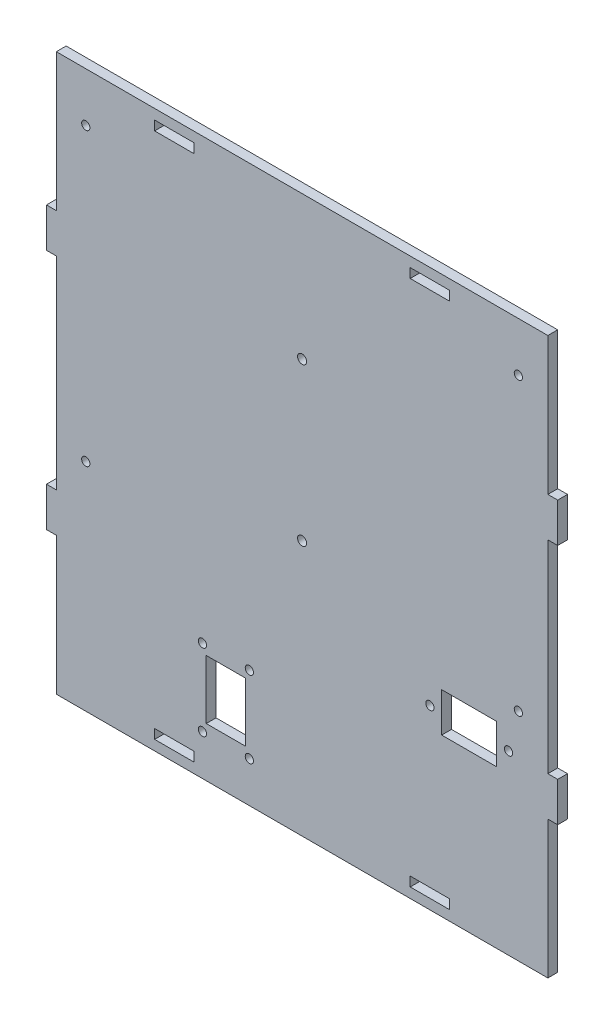
SolidWorks part; units mm, degrees
ref_plane "Front Plane" through (0, 0, 0) normal (0, 0, 1) x (1, 0, 0)
ref_plane "Top Plane" through (0, 0, 0) normal (0, 1, 0) x (1, 0, 0)
ref_plane "Right Plane" through (0, 0, 0) normal (1, 0, 0) x (0, 0, -1)
sketch "Sketch1" plane through (0, 0, 0) normal (0, 0, 1) x (1, 0, 0)
  line L0 (200, 0) -> (250, 0) construction
  line L1 (0, 278) -> (250, 278)
  line L2 (0, 278) -> (0, -5)
  line L3 (0, -5) -> (250, -5)
  line L4 (250, 278) -> (250, -5)
  line L5 (250, 5) -> (250, 0) construction
  line L7 (62, 268) -> (188, 268) construction
  line L8 (50, 0) -> (50, 5) construction
  line L9 (70, 0) -> (70, 5) construction
  line L10 (50, 4.9) -> (70, 4.9)
  line L11 (50, 4.9) -> (50, 0.1)
  line L12 (50, 0.1) -> (70, 0.1)
  line L13 (70, 4.9) -> (70, 0.1)
  line L14 (50, 0) -> (70, 0) construction
  line L15 (180, 0) -> (180, 5) construction
  line L16 (180, 4.9) -> (200, 4.9)
  line L17 (180, 4.9) -> (180, 0.1)
  line L18 (180, 0.1) -> (200, 0.1)
  line L19 (200, 4.9) -> (200, 0.1)
  line L20 (200, 0) -> (200, 5) construction
  line L21 (200, 0) -> (180, 0) construction
  line L22 (0, 5) -> (0, 0) construction
  line L23 (180, 272.9) -> (200, 272.9)
  line L24 (180, 272.9) -> (180, 268.1)
  line L25 (180, 268.1) -> (200, 268.1)
  line L26 (200, 272.9) -> (200, 268.1)
  line L27 (70, 272.9) -> (50, 272.9)
  line L28 (70, 272.9) -> (70, 268.1)
  line L29 (70, 268.1) -> (50, 268.1)
  line L30 (50, 272.9) -> (50, 268.1)
  circle A0 centre (125, 125.1) radius 2.3 construction
  circle A1 centre (125, 205.1) radius 2.3 construction
  circle A2 centre (125, 125.1) radius 2.3
  circle A3 centre (125, 205.1) radius 2.3
  dimension "D1" = 5
  dimension "D2" = 10
  dimension "D3" = 4.8
  dimension "D4" = 0.1
  dimension "D5" = 4.8
  dimension "D6" = 0.1
  dimension "D7" = 4.8
  dimension "D8" = 0.1
  dimension "D9" = 4.8
  dimension "D10" = 0.1
extrude "Boss-Extrude1" add sketch "Sketch1" along normal blind 5
sketch "Sketch2" plane through (0, 0, 5) normal (0, 0, 1) x (1, 0, 0)
  line L0 (0, 278) -> (0, -5) construction
  line L1 (0, 208) -> (-5, 208)
  line L2 (0, 208) -> (0, 188)
  line L3 (0, 188) -> (-5, 188)
  line L4 (-5, 208) -> (-5, 188)
  line L5 (250, -5) -> (250, 278) construction
  line L6 (0, 85) -> (-5, 85)
  line L7 (0, 85) -> (0, 65)
  line L8 (0, 65) -> (-5, 65)
  line L9 (-5, 85) -> (-5, 65)
  line L10 (250, 208) -> (255, 208)
  line L11 (250, 208) -> (250, 188)
  line L12 (250, 188) -> (255, 188)
  line L13 (255, 208) -> (255, 188)
  line L14 (250, 278) -> (0, 278) construction
  line L15 (250, 85) -> (255, 85)
  line L16 (250, 85) -> (250, 65)
  line L17 (250, 65) -> (255, 65)
  line L18 (255, 85) -> (255, 65)
  line L19 (0, -5) -> (250, -5) construction
  dimension "D1" = 5
  dimension "D2" = 20
  dimension "D3" = 70
  dimension "D4" = 70
extrude "Boss-Extrude2" add sketch "Sketch2" against normal up to surface (5 mm away) up to face at (190, 270.5, 0)
sketch "Sketch3" plane through (0, 0, 5) normal (0, 0, 1) x (1, 0, 0)
  line L0 (210, 95) -> (210, 75) construction
  line L1 (196, 95) -> (224, 95)
  line L2 (196, 95) -> (196, 75)
  line L3 (196, 75) -> (224, 75)
  line L4 (224, 95) -> (224, 75)
  line L5 (250, 5) -> (250, 80) construction
  line L6 (0, -5) -> (250, -5) construction
  circle A0 centre (190, 85) radius 2.1
  circle A1 centre (230, 85) radius 2.1
  dimension "D3" = 4.2
  dimension "D4" = 4.2
  dimension "D5" = 40
  dimension "D6" = 20
  dimension "D7" = 10
  dimension "D1" = 28
  dimension "D2" = 20
  dimension "D8" = 40
  dimension "D9" = 80
extrude "Cut-Extrude1" cut sketch "Sketch3" against normal blind 5
sketch "Sketch4" plane through (0, 0, 5) normal (0, 0, 1) x (1, 0, 0)
  line L0 (0, 65) -> (0, -5) construction
  line L1 (76.25, 50.2) -> (96.25, 50.2)
  line L2 (76.25, 50.2) -> (76.25, 20.2)
  line L3 (76.25, 20.2) -> (96.25, 20.2)
  line L4 (96.25, 50.2) -> (96.25, 20.2)
  line L5 (0, -5) -> (250, -5) construction
  dimension "D1" = 20
  dimension "D2" = 30
  dimension "D3" = 76.25
  dimension "D4" = 25.2
extrude "Cut-Extrude2" cut sketch "Sketch4" against normal blind 5
sketch "Sketch5" plane through (0, 0, 5) normal (0, 0, 1) x (1, 0, 0)
  circle A0 centre (98.1863, 15.72) radius 2.1 construction
  circle A1 centre (74.3137, 15.72) radius 2.1 construction
  circle A2 centre (74.3137, 54.68) radius 2.1 construction
  circle A3 centre (98.1863, 54.68) radius 2.1 construction
  circle A4 centre (98.1863, 15.72) radius 2.1
  circle A5 centre (74.3137, 15.72) radius 2.1
  circle A6 centre (74.3137, 54.68) radius 2.1
  circle A7 centre (98.1863, 54.68) radius 2.1
extrude "Cut-Extrude3" cut sketch "Sketch5" against normal through all
sketch "Sketch6" plane through (0, 0, 5) normal (0, 0, 1) x (1, 0, 0)
  line L0 (200, 268) -> (250, 268) construction
  line L1 (250, 208) -> (250, 278) construction
  line L2 (250, -5) -> (250, 278) construction
  line L3 (0, 268) -> (50, 268) construction
  line L4 (0, 258) -> (0, 268) construction
  circle A0 centre (235, 253) radius 2.1
  circle A1 centre (15, 253) radius 2.1
  point P4 (250, 243)
  dimension "D1" = 15
  dimension "D3" = 4.2
  dimension "D4" = 4.2
  dimension "D5" = 15
  dimension "D6" = 15
  dimension "D2" = 15
extrude "Cut-Extrude4" cut sketch "Sketch6" against normal blind 5
sketch "Sketch7" plane through (0, 0, 5) normal (0, 0, 1) x (1, 0, 0)
  line L0 (0, -5) -> (0, 278) construction
  line L1 (0, -5) -> (250, -5) construction
  line L2 (250, 85) -> (250, 188) construction
  circle A0 centre (15, 105) radius 2.1
  circle A1 centre (235, 105) radius 2.1
  dimension "D1" = 4.2
  dimension "D4" = 4.2
  dimension "D5" = 15
  dimension "D6" = 110
  dimension "D2" = 15
  dimension "D3" = 110
extrude "Cut-Extrude5" cut sketch "Sketch7" against normal blind 5
